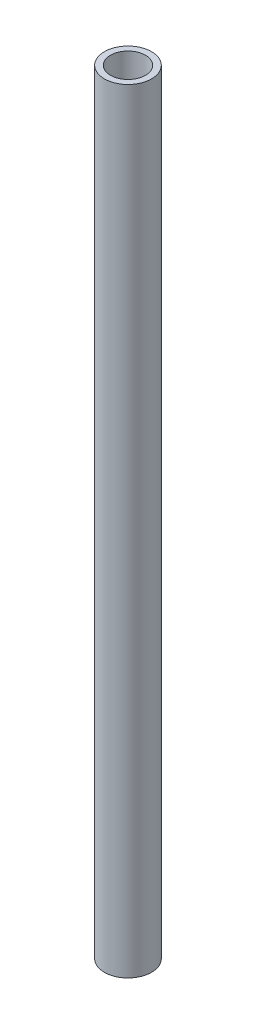
SolidWorks part; units mm, degrees
ref_plane "Front Plane" through (0, 0, 0) normal (0, 0, 1) x (1, 0, 0)
ref_plane "Top Plane" through (0, 0, 0) normal (0, 1, 0) x (1, 0, 0)
ref_plane "Right Plane" through (0, 0, 0) normal (1, 0, 0) x (0, 0, -1)
sketch "Sketch1" plane through (0, 0, 0) normal (0, 1, 0) x (1, 0, 0)
  circle A0 centre (0, 0) radius 7.8994
  circle A1 centre (0, 0) radius 10.668
  dimension "D1" = 15.7988
  dimension "D2" = 21.336
extrude "Boss-Extrude1" add sketch "Sketch1" along normal blind 350
